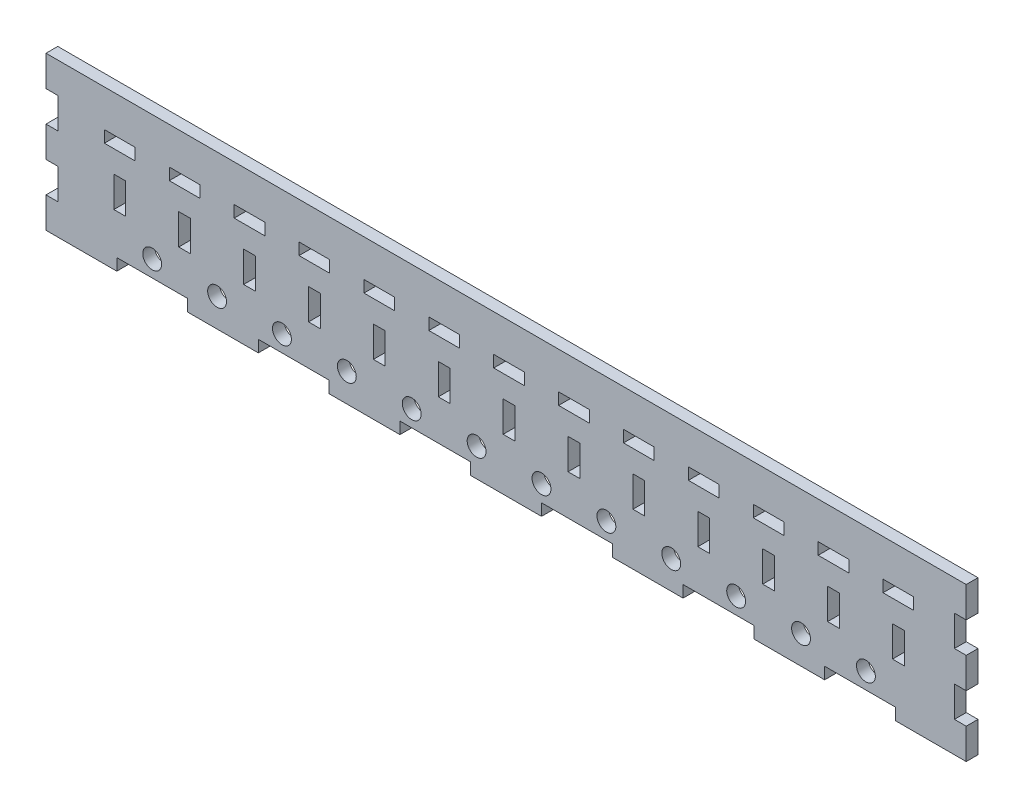
SolidWorks part; units mm, degrees
ref_plane "Plan de face" through (0, 0, 0) normal (0, 0, 1) x (1, 0, 0)
ref_plane "Plan de dessus" through (0, 0, 0) normal (0, 1, 0) x (1, 0, 0)
ref_plane "Plan de droite" through (0, 0, 0) normal (1, 0, 0) x (0, 0, -1)
sketch "Esquisse1" plane through (0, 0, 0) normal (0, 0, 1) x (1, 0, 0)
  line L1 (0, 0) -> (390, 0)
  line L2 (0, 0) -> (0, -65)
  line L3 (0, -65) -> (390, -65)
  line L4 (390, 0) -> (390, -65)
  dimension "D1" = 390
  dimension "D2" = 65
extrude "Boss.-Extru.1" add sketch "Esquisse1" along normal blind 5
sketch "Esquisse2" plane through (0, 0, 5) normal (0, 0, 1) x (1, 0, 0)
  line L0 (0, -65) -> (390, -65) construction
  line L1 (30, -65) -> (60, -65)
  line L2 (30, -65) -> (30, -60)
  line L3 (30, -60) -> (60, -60)
  line L4 (60, -65) -> (60, -60)
  line L5 (0, 0) -> (390, 0) construction
  line L6 (0, 0) -> (0, -65) construction
  dimension "D1" = 390
  dimension "D2" = 30
  dimension "D3" = 30
  dimension "D4" = 5
extrude "Enlèv. mat.-Extru.1" cut sketch "Esquisse2" against normal blind 5
pattern_linear "Répétition linéaire1" count 6 spacing 60 along (1, 0, 0) of "Enlèv. mat.-Extru.1"
sketch "Esquisse3" plane through (0, 0, 5) normal (0, 0, 1) x (1, 0, 0)
  line L0 (0, 0) -> (0, -65) construction
  line L1 (0, -52) -> (5, -52)
  line L2 (0, -52) -> (0, -39)
  line L3 (0, -39) -> (5, -39)
  line L4 (5, -52) -> (5, -39)
  line L5 (0, 0) -> (0, -65) construction
  line L6 (0, -65) -> (30, -65) construction
  dimension "D4" = 5
  dimension "D1" = 65
  dimension "D2" = 13
  dimension "D3" = 13
extrude "Enlèv. mat.-Extru.2" cut sketch "Esquisse3" against normal blind 5
pattern_linear "Répétition linéaire2" count 2 spacing 26 along (0, 1, 0) of "Enlèv. mat.-Extru.2"
ref_plane "Plan1" through (195, 0, 0) normal (-1, 0, 0) x (0, 0, 1)
mirror "Symétrie1" about plane through (195, 0, 0) normal (-1, 0, 0) of "Répétition linéaire2", "Enlèv. mat.-Extru.2"
sketch "Esquisse5" plane through (0, 0, 5) normal (0, 0, 1) x (1, 0, 0)
  line L2 (0, -26) -> (0, -39) construction
  line L4 (0, -65) -> (30, -65) construction
  circle A0 centre (100, -53) radius 4
  dimension "D3" = 8
  dimension "D1" = 100
  dimension "D2" = 12
extrude "Enlèv. mat.-Extru.4" cut sketch "Esquisse5" against normal blind 5
pattern_linear "Répétition linéaire4" count 10 spacing 27.5 along (1, 0, 0) count 3 spacing 27.5 along (-1, 0, 0) of "Enlèv. mat.-Extru.4"
sketch "Esquisse4" plane through (0, 0, 5) normal (0, 0, 1) x (1, 0, 0)
  line L0 (100, -53) -> (100, -38.7277) construction
  line L1 (83.75, -30) -> (88.75, -30)
  line L2 (83.75, -30) -> (83.75, -43)
  line L3 (83.75, -43) -> (88.75, -43)
  line L4 (88.75, -30) -> (88.75, -43)
  line L7 (60, -65) -> (90, -65) construction
  line L11 (86.25, -15.65) -> (86.25, -20.65) construction
  line L12 (79.75, -15.65) -> (92.75, -15.65)
  line L13 (79.75, -15.65) -> (79.75, -20.65)
  line L14 (79.75, -20.65) -> (92.75, -20.65)
  line L15 (92.75, -15.65) -> (92.75, -20.65)
  line L16 (86.25, -30) -> (86.25, -43) construction
  line L17 (120, -60) -> (90, -60) construction
  point P6 (86.25, -30)
  point P9 (100, -53)
  dimension "D2" = 13
  dimension "D3" = 5
  dimension "D4" = 35
  dimension "D1" = 11.25
  dimension "D5" = 13
  dimension "D6" = 5
  dimension "D7" = 39.35
extrude "Enlèv. mat.-Extru.3" cut sketch "Esquisse4" against normal blind 5
pattern_linear "Répétition linéaire3" count 3 spacing 27.5 along (-1, 0, 0) count 11 spacing 27.5 along (1, 0, 0) of "Enlèv. mat.-Extru.3"
equation "\"D1@Esquisse1\"=400-10"
equation "\"D2@Esquisse2\"=\"D1@Esquisse2\"/13"
equation "\"D3@Esquisse2\"=\"D1@Esquisse2\"/13"
equation "\"D2@Esquisse3\"=\"D1@Esquisse3\"/5"
equation "\"D3@Esquisse3\"=\"D1@Esquisse3\"/5"
equation "\"D1@Esquisse4\"=22.5/2"
